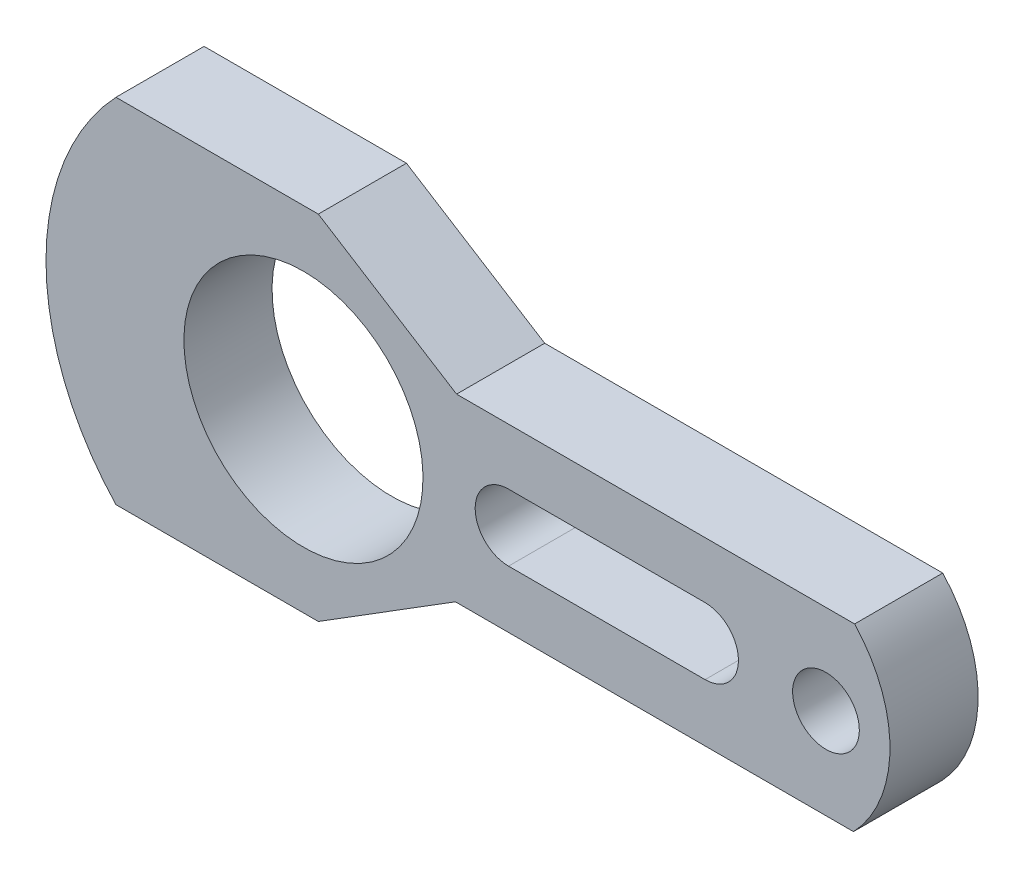
SolidWorks part; units mm, degrees
material "Aleación 1060"
ref_plane "Alzado" through (0, 0, 0) normal (0, 0, 1) x (1, 0, 0)
ref_plane "Planta" through (0, 0, 0) normal (0, 1, 0) x (1, 0, 0)
ref_plane "Vista lateral" through (0, 0, 0) normal (1, 0, 0) x (0, 0, -1)
sketch "Croquis1" plane through (0, 0, 0) normal (0, 0, 1) x (1, 0, 0)
  line L0 (50.8412, -86.861) -> (100.076, -8.4341)
  line L1 (0, -116.332) -> (0, -227.838) construction
  line L2 (18.923, -116.332) -> (18.923, -227.838)
  line L3 (-18.923, -116.332) -> (-18.923, -227.838)
  line L4 (-51.5208, -312.0231) -> (-51.5208, -86.2171)
  line L5 (50.8412, -312.667) -> (50.8412, -86.861)
  line L6 (-100.076, 106.3739) -> (-100.076, -8.4341)
  line L7 (-100.076, -8.4341) -> (-51.5208, -86.2171)
  line L9 (100.076, 106.3739) -> (100.076, -8.4341)
  circle A0 centre (0, 0) radius 67.818
  arc A2 (-51.5208, -312.0231) -> (50.8412, -312.667) centre (0, -258.318) ccw
  arc A3 (18.923, -116.332) -> (-18.923, -116.332) centre (0, -116.332) ccw
  arc A4 (-18.923, -227.838) -> (18.923, -227.838) centre (0, -227.838) ccw
  circle A5 centre (0, -296.418) radius 18.923
  arc A6 (100.076, 106.3739) -> (-100.076, 106.3739) centre (0, 0) ccw
  point P10 (0, -172.085)
  dimension "D1" = 135.636
  dimension "D2" = 146.05
  dimension "D4" = 211.974
  dimension "D9" = 91.694
  dimension "D10" = 225.806
  dimension "D11" = 225.806
  dimension "D14" = 172.085
  dimension "D13" = 18.923
  dimension "D16" = 74.422
  dimension "D17" = 38.1
  dimension "D21" = 50.8412
  dimension "D3" = 200.152
  dimension "D6" = 114.808
  dimension "D7" = 114.808
  dimension "D12" = 111.506
  dimension "D18" = 102.362
  dimension "D19" = 100.076
  dimension "D20" = 31.9182
extrude "Saliente-Extruir1" add sketch "Croquis1" along normal blind 50
move or copy body "Corps-Déplacer/Copier1" bodies to move or copy 105 copy no rotation origin (0, 0, 0) rotation axis (0, 0, 1) rotation angle 90
